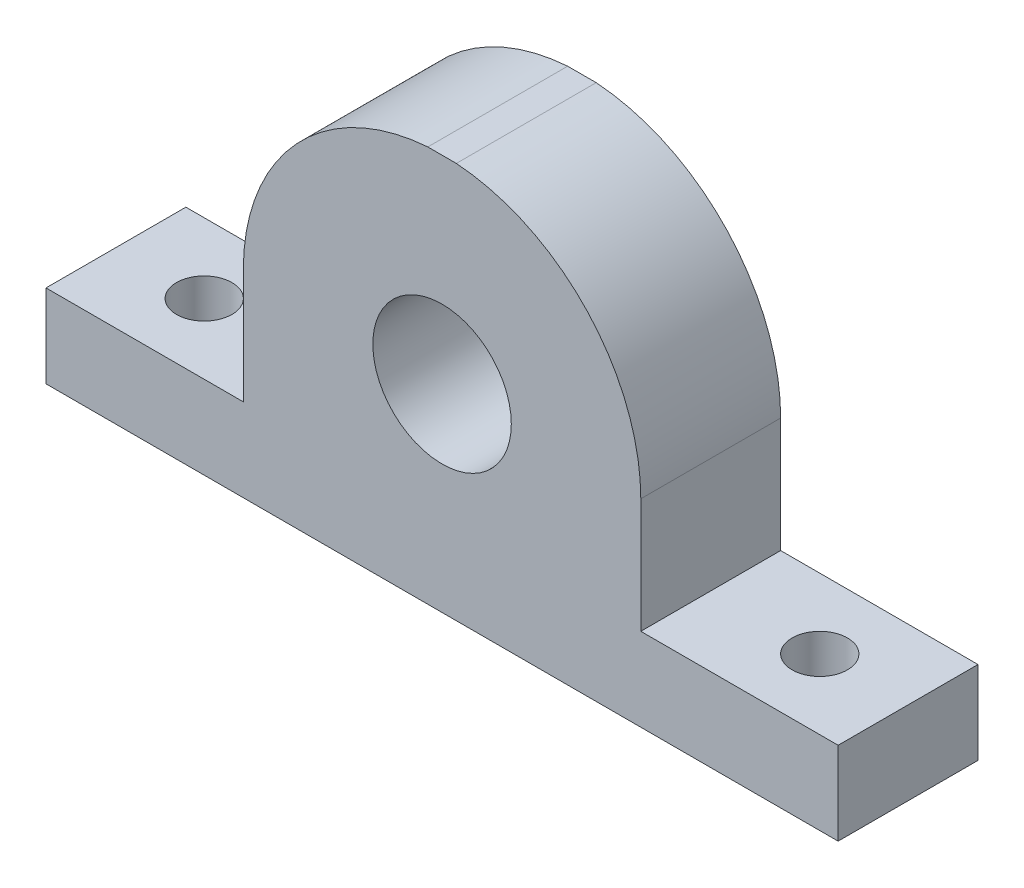
SolidWorks part; units mm, degrees
ref_plane "Front Plane" through (0, 0, 0) normal (0, 0, 1) x (1, 0, 0)
ref_plane "Top Plane" through (0, 0, 0) normal (0, 1, 0) x (1, 0, 0)
ref_plane "Right Plane" through (0, 0, 0) normal (1, 0, 0) x (0, 0, -1)
sketch "Sketch1" plane through (0, 0, 0) normal (0, 0, 1) x (1, 0, 0)
  line L1 (0, 0) -> (57.2, 0)
  line L2 (0, 0) -> (0, 28.6)
  line L3 (0, 28.6) -> (57.2, 28.6)
  line L4 (57.2, 0) -> (57.2, 28.6)
  dimension "D1" = 57.2
  dimension "D2" = 28.6
extrude "Boss-Extrude1" add sketch "Sketch1" along normal blind 10.1
sketch "Sketch3" plane through (0, 0, 10.1) normal (0, 0, 1) x (1, 0, 0)
  line L0 (28.6, 28.6) -> (28.6, 0) construction
  line L1 (57.2, 28.6) -> (0, 28.6) construction
  line L2 (0, 0) -> (57.2, 0) construction
  circle A0 centre (28.6, 14.287) radius 5
  dimension "D1" = 10
extrude "Cut-Extrude2" cut sketch "Sketch3" against normal through all
sketch "Sketch4" plane through (0, 0, 10.1) normal (0, 0, 1) x (1, 0, 0)
  line L0 (0, 5.9991) -> (14.25, 5.9991)
  line L1 (14.25, 5.9991) -> (14.25, 14.287)
  line L2 (42.95, 14.287) -> (42.95, 5.9991)
  line L3 (42.95, 5.9991) -> (57.2191, 5.9991)
  arc A1 (14.25, 14.287) -> (42.95, 14.287) centre (28.6, 14.287) cw
extrude "Cut-Extrude3" cut sketch "Sketch4" against normal through all and the other way through all
sketch "Sketch5" plane through (0, 5.9991, 0) normal (0, 1, 0) x (-1, 0, 0)
  line L0 (0, 10.1) -> (0, 0) construction
  line L1 (-14.25, 5.05) -> (0, 5.05) construction
  line L2 (-14.25, 10.1) -> (-14.25, 0) construction
  line L3 (-6.375, 10.1) -> (-6.375, 0)
  line L4 (-57.2, 5.05) -> (-42.95, 5.05) construction
  line L5 (-57.2, 10.1) -> (-57.2, 0) construction
  line L6 (-42.95, 10.1) -> (-42.95, 0) construction
  line L7 (-57.2, 0) -> (-57.2, 10.1) construction
  line L8 (-50.825, 0) -> (-50.825, 10.1)
  circle A0 centre (-6.375, 5.05) radius 2
  circle A1 centre (-50.825, 5.05) radius 2
  dimension "D2" = 6.375
  dimension "D1" = 6.375
extrude "Cut-Extrude4" cut sketch "Sketch5" against normal through all contours A1 | A0
